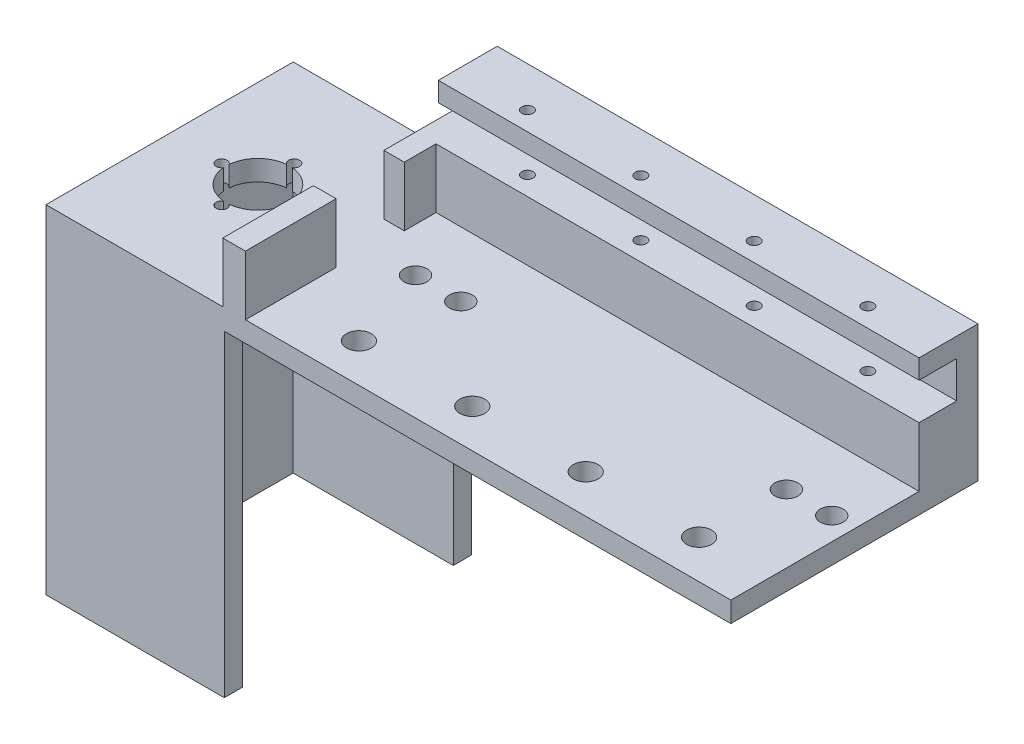
SolidWorks part; units mm, degrees
ref_plane "Front Plane" through (0, 0, 0) normal (0, 0, 1) x (1, 0, 0)
ref_plane "Top Plane" through (0, 0, 0) normal (0, 1, 0) x (1, 0, 0)
ref_plane "Right Plane" through (0, 0, 0) normal (1, 0, 0) x (0, 0, -1)
sketch "Sketch4" plane through (0, 0, 0) normal (0, 0, 1) x (1, 0, 0)
  line L1 (-89.891, -20.3228) -> (16.109, -20.3228)
  line L2 (-89.891, -20.3228) -> (-89.891, -50.3228)
  line L3 (-89.891, -50.3228) -> (16.109, -50.3228)
  line L4 (16.109, -20.3228) -> (16.109, -50.3228)
  dimension "D1" = 30
  dimension "D2" = 106
extrude "Boss-Extrude2" add sketch "Sketch4" against normal blind 13
sketch "Sketch25" plane through (0, 0, 0) normal (0, 0, 1) x (1, 0, 0)
  line L0 (-89.891, -20.3228) -> (-89.891, -50.3228) construction
  line L1 (-89.891, -24.6013) -> (16.109, -24.6013)
  line L2 (-89.891, -24.6013) -> (-89.891, -32.7013)
  line L3 (-89.891, -32.7013) -> (16.109, -32.7013)
  line L4 (16.109, -24.6013) -> (16.109, -32.7013)
  line L5 (16.109, -50.3228) -> (16.109, -20.3228) construction
extrude "Cut-Extrude3" cut sketch "Sketch25" against normal blind 8.3 and the other way through all
hole_wizard "M3x0.5 Tapped Hole1" positions "3DSketch1" profile "Sketch27" tap size "M3x0.5" standard "ANSI Metric" end condition through all
sketch3d "3DSketch1"
  line L0 (16.109, -20.3228, -13) -> (16.109, -20.3228, 0) construction
  line L2 (16.109, -20.3228, 0) -> (-89.891, -20.3228, 0) construction
  line L3 (-89.891, -20.3228, -13) -> (-89.891, -20.3228, 0) construction
  point P0 (-74.391, -20.3228, -4.15)
  point P2 (-49.391, -20.3228, -4.15)
  point P4 (0.609, -20.3228, -4.2057)
  point P6 (-24.391, -20.3228, -4.15)
  dimension "D1" = 15.5
  dimension "D2" = 25
  dimension "D5" = 4.15
  dimension "D6" = 4.15
  dimension "D7" = 4.15
  dimension "D8" = 25
  dimension "D9" = 25
  dimension "D10" = 15.5001
cosmetic thread "Hole Thread2" parameters "D1"=6, "D2"=3
cosmetic thread "Hole Thread3" parameters "D1"=6, "D2"=3
cosmetic thread "Hole Thread4" parameters "D1"=6, "D2"=3
cosmetic thread "Hole Thread5" parameters "D1"=6, "D2"=3
sketch "Sketch27" plane through (-74.391, -20.3228, -4.15) normal (1, 0, 0) x (0, 0, 1)
  line L0 (0, 0) -> (0, 30)
  line L1 (0, 30) -> (1.25, 30)
  line L2 (1.25, 30) -> (1.25, 0)
  line L5 (1.25, 0) -> (0, 0)
  line L11 (0, -6.35) -> (0, 107.95) construction
  dimension "Thru Tap Drill Dia." = 2.5
  dimension "Thru Tap Drill Depth" = 30
sketch "Sketch28" plane through (0, 0, 0) normal (0, 0, 1) x (1, 0, 0)
  line L0 (-89.891, -32.7013) -> (-89.891, -50.3228) construction
  line L1 (-89.891, -45.8228) -> (16.109, -45.8228)
  line L2 (-89.891, -45.8228) -> (-89.891, -50.3228)
  line L3 (-89.891, -50.3228) -> (16.109, -50.3228)
  line L4 (16.109, -45.8228) -> (16.109, -50.3228)
  dimension "D1" = 4.5
extrude "Boss-Extrude3" add sketch "Sketch28" along normal blind 41.5
sketch "Sketch32" plane through (-89.891, 0, 0) normal (-1, 0, 0) x (0, 0, 1)
  line L1 (0, -45.8228) -> (41.5, -45.8228)
  line L2 (0, -45.8228) -> (0, -50.3228)
  line L3 (0, -50.3228) -> (41.5, -50.3228)
  line L4 (41.5, -45.8228) -> (41.5, -50.3228)
extrude "Boss-Extrude10" add sketch "Sketch32" along normal blind 5
sketch "Sketch33" plane through (-89.891, 0, 0) normal (-1, 0, 0) x (0, 0, 1)
  line L1 (0, -32.7013) -> (-13, -32.7013)
  line L2 (0, -32.7013) -> (0, -50.3228)
  line L3 (0, -50.3228) -> (-13, -50.3228)
  line L4 (-13, -32.7013) -> (-13, -50.3228)
extrude "Boss-Extrude12" add sketch "Sketch33" along normal blind 5
sketch "Sketch34" plane through (0, 0, 0) normal (0, 0, 1) x (1, 0, 0)
  line L0 (16.109, -45.8228) -> (-94.891, -45.8228) construction
  line L1 (-94.891, -32.7013) -> (-90.3922, -32.7013)
  line L2 (-94.891, -32.7013) -> (-94.891, -45.8228)
  line L3 (-94.891, -45.8228) -> (-90.3922, -45.8228)
  line L4 (-90.3922, -32.7013) -> (-90.3922, -45.8228)
extrude "Boss-Extrude13" add sketch "Sketch34" along normal blind 7
sketch "Sketch35" plane through (-94.891, 0, 0) normal (-1, 0, 0) x (0, 0, 1)
  line L1 (41.5, -45.8228) -> (-13, -45.8228)
  line L2 (41.5, -45.8228) -> (41.5, -50.3228)
  line L3 (41.5, -50.3228) -> (-13, -50.3228)
  line L4 (-13, -45.8228) -> (-13, -50.3228)
extrude "Boss-Extrude14" add sketch "Sketch35" along normal blind 40
sketch "Sketch36" plane through (0, -45.8228, 0) normal (0, 1, 0) x (1, 0, 0)
  line L0 (16.109, -41.5) -> (-134.891, -41.5) construction
  line L1 (-90.9181, -41.5) -> (-95.9181, -41.5)
  line L2 (-90.9181, -41.5) -> (-90.9181, -21.5)
  line L3 (-90.9181, -21.5) -> (-95.9181, -21.5)
  line L4 (-95.9181, -41.5) -> (-95.9181, -21.5)
  dimension "D1" = 5
  dimension "D2" = 20
extrude "Boss-Extrude15" add sketch "Sketch36" along normal blind 13.12 contours L2 L3 L4 L1
hole_wizard "#8 (0.199) Diameter Hole1" positions "3DSketch3" profile "Sketch38" hole size "#8" standard "Progressive" end condition through all
sketch3d "3DSketch3"
  line L0 (16.109, -45.8228, 41.5) -> (-90.9181, -45.8228, 41.5) construction
  line L1 (16.109, -45.8228, 41.5) -> (16.109, -45.8228, 0) construction
  point P0 (-80.6691, -45.8228, 14.25)
  point P2 (11.109, -45.8228, 14.25)
  point P4 (1.109, -45.8228, 14.25)
  point P6 (-70.6691, -45.8228, 14.25)
  dimension "D1" = 27.25
  dimension "D2" = 27.25
  dimension "D3" = 27.25
  dimension "D4" = 27.25
  dimension "D5" = 10
  dimension "D6" = 10
  dimension "D7" = 5
sketch "Sketch38" plane through (-80.6691, -45.8228, 14.25) normal (1, 0, 0) x (0, 0, 1)
  line L0 (0, 0) -> (0, 4.5)
  line L1 (0, 4.5) -> (2.5273, 4.5)
  line L2 (2.5273, 4.5) -> (2.5273, 0)
  line L5 (2.5273, 0) -> (0, 0)
  line L11 (0, -6.35) -> (0, 107.95) construction
  dimension "Thru Hole Dia." = 5.0546
  dimension "Thru Hole Depth" = 4.5
sketch "Sketch39" plane through (0, -45.8228, 0) normal (0, 1, 0) x (1, 0, 0)
  line L1 (-95.9181, -41.5) -> (-95.9181, -21.5) construction
  line L2 (-134.891, -41.5) -> (-134.891, 13) construction
  line L3 (-134.891, 13) -> (-94.891, 13) construction
  circle A0 centre (-115.4181, -14.25) radius 7
  dimension "D1" = 19.5
  dimension "D2" = 19.4729
  dimension "D3" = 27.25
extrude "Cut-Extrude4" cut sketch "Sketch39" against normal blind 10 contours A0
hole_wizard "M2 Clearance Hole1" positions "3DSketch4" profile "Sketch40" hole size "M2" standard "ANSI Metric" end condition through all
sketch3d "3DSketch4"
  line L0 (-134.891, -45.8228, 41.5) -> (-134.891, -45.8228, -13) construction
  line L1 (-95.9181, -45.8228, 41.5) -> (-134.891, -45.8228, 41.5) construction
  line L3 (-95.9181, -45.8228, 41.5) -> (-95.9181, -45.8228, 21.5) construction
  point P0 (-107.4181, -45.8228, 14.25)
  point P2 (-115.421, -45.8228, 22.25)
  point P4 (-115.421, -45.8228, 6.25)
  point P6 (-123.4181, -45.8228, 14.25)
  point P19 (-115.4046, -45.8228, 41.5)
  dimension "D1" = 19.47
  dimension "D2" = 19.47
  dimension "D3" = 16
  dimension "D4" = 27.25
  dimension "D5" = 27.25
  dimension "D6" = 19.25
  dimension "D7" = 16
  dimension "D8" = 11.5
  dimension "D9" = 11.4729
sketch "Sketch40" plane through (-107.4181, -45.8228, 14.25) normal (1, 0, 0) x (0, 0, 1)
  line L0 (0, 0) -> (0, 4.5)
  line L1 (0, 4.5) -> (1.2, 4.5)
  line L2 (1.2, 4.5) -> (1.2, 0)
  line L5 (1.2, 0) -> (0, 0)
  line L11 (0, -6.35) -> (0, 107.95) construction
  dimension "Thru Hole Dia." = 2.4
  dimension "Thru Hole Depth" = 4.5
hole_wizard "M5 Clearance Hole1" positions "3DSketch5" profile "Sketch41" hole size "M5" standard "ANSI Metric" end condition through all
sketch3d "3DSketch5"
  line L0 (16.109, -50.3228, -13) -> (16.109, -50.3228, 41.5) construction
  line L1 (-134.891, -50.3228, 41.5) -> (16.109, -50.3228, 41.5) construction
  point P0 (0.609, -50.3228, 33)
  point P2 (-24.391, -50.3228, 33)
  point P4 (-49.391, -50.3228, 33)
  point P6 (-74.391, -50.3228, 33)
  dimension "D1" = 15.5
  dimension "D2" = 8.5
  dimension "D3" = 25
  dimension "D4" = 8.5
  dimension "D5" = 25
  dimension "D6" = 8.5
  dimension "D7" = 25
  dimension "D8" = 8.5
sketch "Sketch41" plane through (0.609, -50.3228, 33) normal (1, 0, 0) x (0, 0, -1)
  line L0 (0, 0) -> (0, 30)
  line L1 (0, 30) -> (2.75, 30)
  line L2 (2.75, 30) -> (2.75, 0)
  line L5 (2.75, 0) -> (0, 0)
  line L11 (0, -6.35) -> (0, 107.95) construction
  dimension "Thru Hole Dia." = 5.5
  dimension "Thru Hole Depth" = 30
sketch "Sketch43" plane through (0, -50.3228, 0) normal (0, -1, 0) x (-1, 0, 0)
  line L0 (134.891, -41.5) -> (-16.109, -41.5) construction
  line L1 (95.5862, -41.5) -> (134.891, -41.5)
  line L2 (95.5862, -41.5) -> (95.5862, -37.5)
  line L3 (95.5862, -37.5) -> (134.891, -37.5)
  line L4 (134.891, -41.5) -> (134.891, -37.5)
  line L5 (134.891, 13) -> (134.891, -41.5) construction
  line L6 (134.891, 13) -> (-16.109, 13) construction
  line L7 (134.891, -37.5) -> (130.891, -37.5)
  line L8 (134.891, -37.5) -> (134.891, 13)
  line L9 (134.891, 13) -> (130.891, 13)
  line L10 (130.891, -37.5) -> (130.891, 13)
  line L12 (95.5862, 13) -> (130.891, 13)
  line L13 (95.5862, 13) -> (95.5862, 9)
  line L14 (95.5862, 9) -> (130.891, 9)
  line L15 (130.891, 13) -> (130.891, 9)
  line M8 (-16.109, -41.5) -> (134.891, -41.5)
  line M9 (134.891, -41.5) -> (134.891, 13)
  line M10 (134.891, 13) -> (-16.109, 13)
  dimension "D1" = 4
  dimension "D2" = 4
  dimension "D3" = 4
extrude "Boss-Extrude16" add sketch "Sketch43" along normal blind 70 contours L3 L2 M8 M9 | L10 L3 M9 M10 | L15 L14 L13 L12
